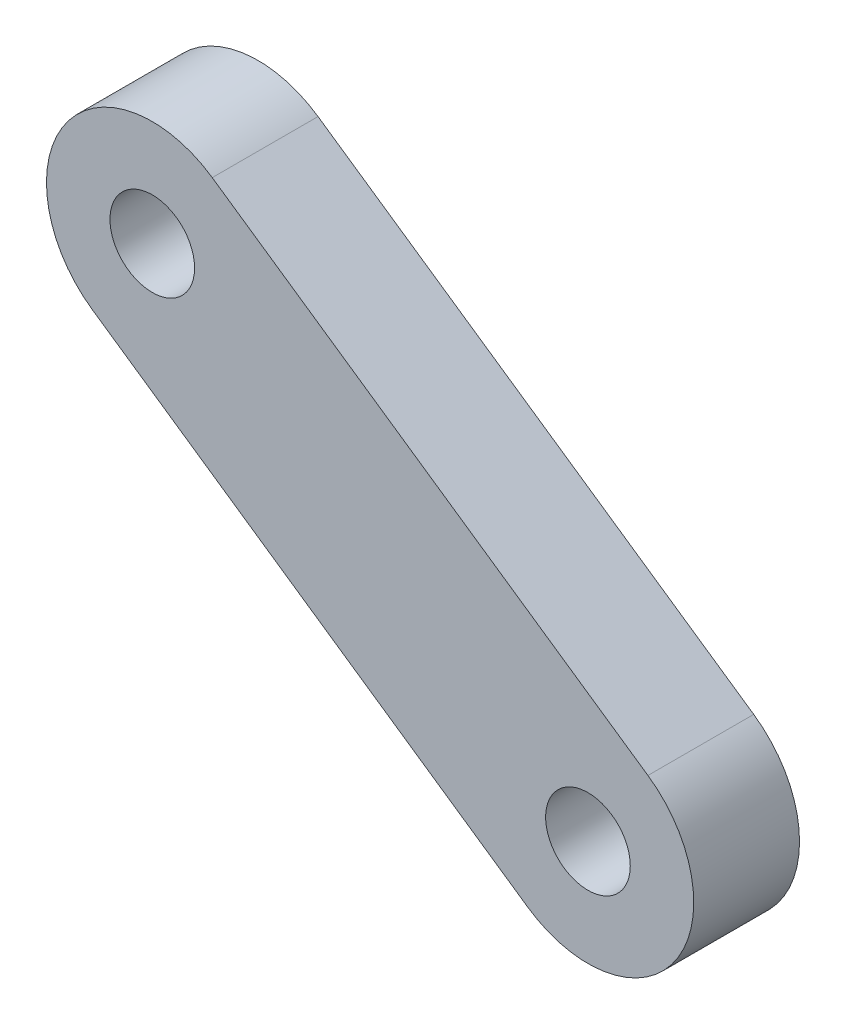
SolidWorks part; units mm, degrees
ref_plane "Front Plane" through (0, 0, 0) normal (0, 0, 1) x (1, 0, 0)
ref_plane "Top Plane" through (0, 0, 0) normal (0, 1, 0) x (1, 0, 0)
ref_plane "Right Plane" through (0, 0, 0) normal (1, 0, 0) x (0, 0, -1)
sketch "Sketch1" plane through (0, 0, 0) normal (0, 0, 1) x (0.9998, -0.022, 0)
  line L0 (0.6447, 52.8572) -> (-25.8837, 70.342) construction
  line L1 (5.01, 49.98) -> (5.01, 69.98) construction
  line L2 (5.01, 69.98) -> (-55.6789, 69.98) construction
  line L3 (-46.2352, 83.6971) -> (-25.3345, 69.98) construction
  line L4 (-46.2352, 83.6971) -> (-43.4918, 87.8772) construction
  line L5 (-43.4918, 87.8772) -> (-48.9786, 79.5169) construction
  line L6 (-43.4918, 87.8772) -> (-22.591, 74.1602)
  line L7 (-48.9786, 79.5169) -> (-28.0779, 65.7999)
  line L8 (-22.591, 74.1602) -> (-28.0779, 65.7999) construction
  circle A0 centre (5.01, 49.98) radius 2 construction
  circle A1 centre (5.01, 49.98) radius 2 construction
  circle A3 centre (-25.3345, 69.98) radius 2
  arc A4 (-29.5092, 72.7316) -> (-29.5146, 72.7234) centre (-25.3345, 69.98) ccw
  circle A5 centre (-46.2352, 83.6971) radius 2 construction
  circle A6 centre (-46.2352, 83.6971) radius 2
  arc A7 (-43.4918, 87.8772) -> (-48.9786, 79.5169) centre (-46.2352, 83.6971) ccw
  arc A8 (-28.0779, 65.7999) -> (-22.591, 74.1602) centre (-25.3345, 69.98) ccw
  point P18 (-25.3345, 69.98)
  dimension "D1" = 5
  dimension "D2" = 5
  dimension "D4" = 4
  dimension "D5" = 4
  dimension "D6" = 10
  dimension "D3" = 20
  dimension "D7" = 25
extrude "Boss-Extrude1" add sketch "Sketch1" along normal blind 5
